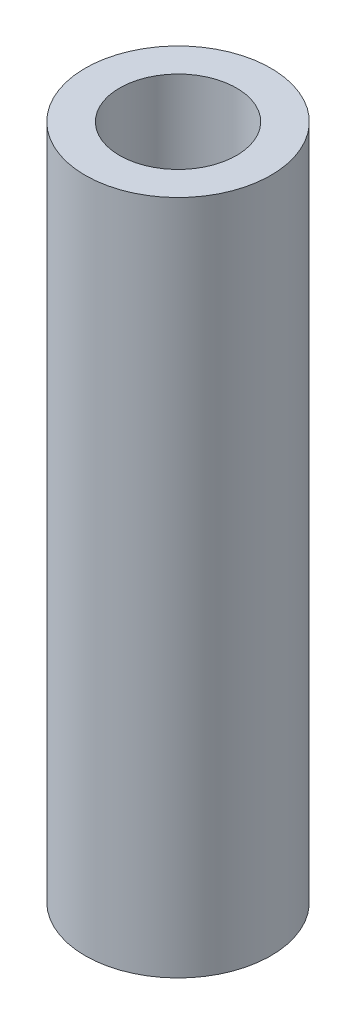
SolidWorks part; units mm, degrees
material "6061-T6 (SS)"
ref_plane "X-Y Datum" through (0, 0, 0) normal (0, 0, 1) x (1, 0, 0)
ref_plane "X-Z Datum" through (0, 0, 0) normal (0, 1, 0) x (1, 0, 0)
ref_plane "Y-Z Datum" through (0, 0, 0) normal (1, 0, 0) x (0, 0, -1)
sketch "Sketch1" plane through (0, 0, 0) normal (0, 1, 0) x (1, 0, 0)
  circle A0 centre (0, 0) radius 3.175
  circle A1 centre (0, 0) radius 2
  dimension "D1" = 6.35
  dimension "D2" = 4
extrude "Boss-Extrude1" add sketch "Sketch1" against normal blind 23.114
